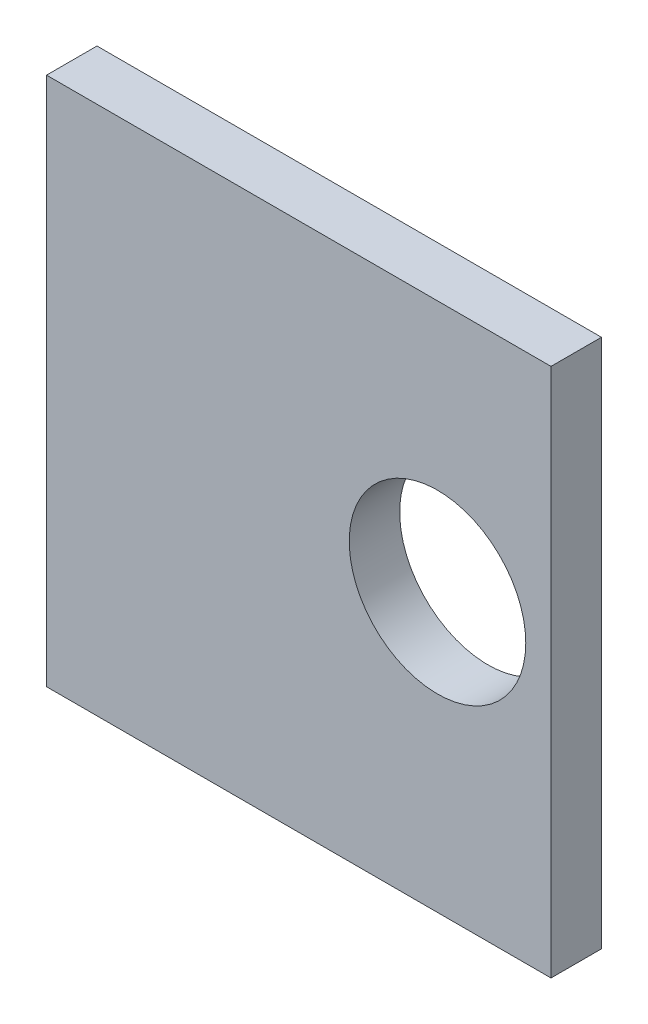
SolidWorks part; units mm, degrees
material "6061-T6 (SS)"
ref_plane "Front Plane" through (0, 0, 0) normal (0, 0, 1) x (1, 0, 0)
ref_plane "Top Plane" through (0, 0, 0) normal (0, 1, 0) x (1, 0, 0)
ref_plane "Right Plane" through (0, 0, 0) normal (1, 0, 0) x (0, 0, -1)
sketch "Sketch1" plane through (0, 0, 0) normal (0, 0, 1) x (1, 0, 0)
  line L0 (-33.3375, -991.7963) -> (-33.3375, 48344.9928) construction
  line L1 (-49.2125, 31.75) -> (14.2875, 31.75)
  line L2 (-49.2125, 31.75) -> (-49.2125, -34.925)
  line L3 (-49.2125, -34.925) -> (14.2875, -34.925)
  line L4 (14.2875, 31.75) -> (14.2875, -34.925)
  line L5 (-26.9875, -992.522) -> (-26.9875, 48344.2671) construction
  circle A0 centre (0, 0) radius 11.1125
  circle A1 centre (0, 0) radius 31.75 construction
  dimension "D4" = 22.225
  dimension "D5" = 63.5
  dimension "D6" = 3.175
  dimension "D7" = 3.175
  dimension "D1" = 6.35
  dimension "D2" = 22.225
  dimension "D3" = 49.2125
  dimension "D8" = 66.675
extrude "Boss-Extrude1" add sketch "Sketch1" along normal blind 6.35
